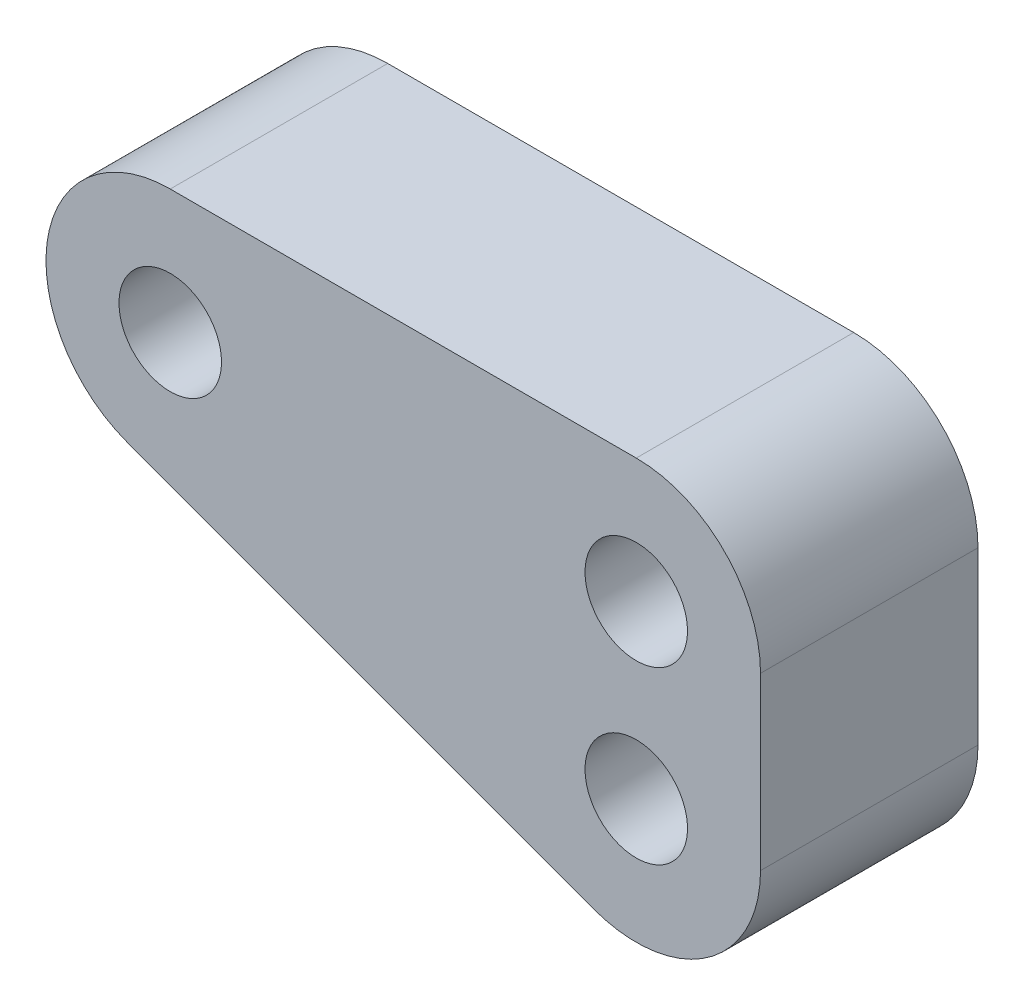
SolidWorks part; units mm, degrees
ref_plane "Plan de face" through (0, 0, 0) normal (0, 0, 1) x (1, 0, 0)
ref_plane "Plan de dessus" through (0, 0, 0) normal (0, 1, 0) x (1, 0, 0)
ref_plane "Plan de droite" through (0, 0, 0) normal (1, 0, 0) x (0, 0, -1)
sketch "Esquisse1" plane through (0, 0, 0) normal (0, 0, 1) x (1, 0, 0)
  line L0 (-15, 4) -> (0, 4)
  line L1 (4, 0) -> (4, -5.5)
  line L2 (-1.377, -9.2555) -> (-16.377, -3.7555)
  arc A0 (4, -5.5) -> (-1.377, -9.2555) centre (0, -5.5) cw
  arc A1 (0, 4) -> (4, 0) centre (0, 0) cw
  arc A2 (-15, 4) -> (-16.377, -3.7555) centre (-15, 0) ccw
  point P2 (0, 0)
  point P4 (0, 0)
  point P5 (0, 0)
  point P6 (0, 0)
  point P13 (0, 0)
  point P14 (4.8807, 4.8214)
  point P15 (0, 0)
  point P17 (0, 0)
  dimension "D1" = 4
  dimension "D2" = 15
  dimension "D3" = 5.5
extrude "Boss.-Extru.1" add sketch "Esquisse1" along normal blind 7
hole_wizard "Trou taraudé M41" positions "Esquisse2" profile "Esquisse3" tap size "M4" standard "ISO" end condition through all
sketch "Esquisse2" plane through (0, 0, 0) normal (0, 0, 1) x (1, 0, 0)
  point P0 (-15, 0)
  point P3 (0, 0)
  point P6 (0, -5.5)
sketch "Esquisse3" plane through (-15, 0, 0) normal (1, 0, 0) x (0, 1, 0)
  line L0 (0, 0) -> (0, 7)
  line L1 (0, 7) -> (1.65, 7)
  line L2 (1.65, 7) -> (1.65, 0)
  line L5 (1.65, 0) -> (0, 0)
  line L11 (0, -6.35) -> (0, 107.95) construction
  dimension "Diamètre du trou pour taraudage jusqu'au prochain" = 3.3
  dimension "Profondeur du trou pour taraudage jusqu'au prochain" = 7
cosmetic thread "Filetage de perçage1"
cosmetic thread "Filetage de perçage2"
cosmetic thread "Filetage de perçage3"
